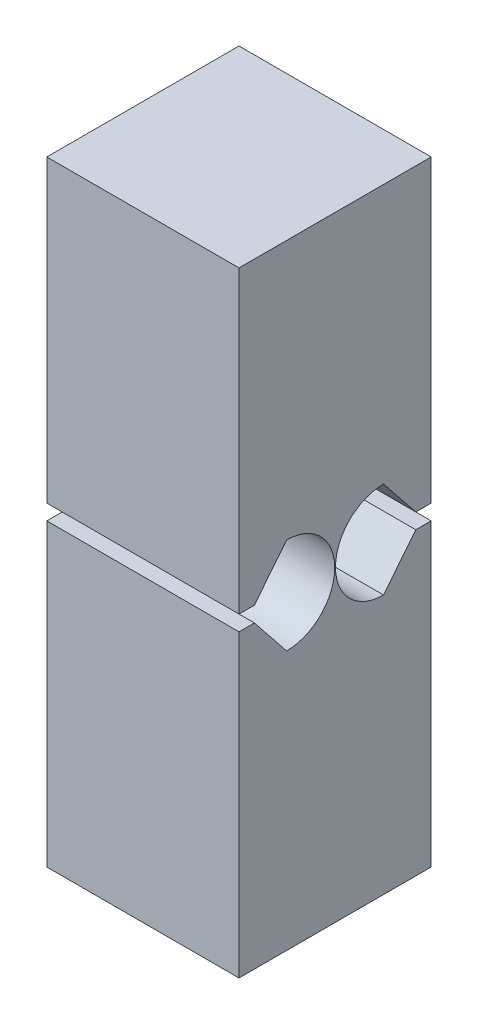
SolidWorks part; units mm, degrees
material "Beryllium Copper, UNS C17200"
ref_plane "Front Plane" through (0, 0, 0) normal (0, 0, 1) x (1, 0, 0)
ref_plane "Top Plane" through (0, 0, 0) normal (0, 1, 0) x (1, 0, 0)
ref_plane "Right Plane" through (0, 0, 0) normal (1, 0, 0) x (0, 0, -1)
sketch "Sketch1" plane through (0, 0, 0) normal (0, 1, 0) x (1, 0, 0)
  line L1 (-3.175, 3.175) -> (3.175, 3.175)
  line L2 (-3.175, 3.175) -> (-3.175, -3.175)
  line L3 (-3.175, -3.175) -> (3.175, -3.175)
  line L4 (3.175, 3.175) -> (3.175, -3.175)
  dimension "D1" = 3.175
  dimension "D2" = 3.175
  dimension "D3" = 3.175
  dimension "D4" = 3.175
extrude "Boss-Extrude1" add sketch "Sketch1" along normal mid plane 20.32
sketch "Sketch2" plane through (3.175, 0, 0) normal (1, 0, 0) x (0, 0, -1)
  line L0 (-3.175, 0.254) -> (-3.175, -0.254)
  line L1 (-3.175, 10.16) -> (-3.175, -10.16) construction
  line L2 (-3.175, -0.254) -> (-2.667, -0.254)
  line L3 (-2.667, -0.254) -> (-1.6002, -1.5875)
  line L4 (-3.175, 0.254) -> (-2.667, 0.254)
  line L5 (-2.667, 0.254) -> (-1.6002, 1.5875)
  arc A0 (-1.6002, 1.5875) -> (-1.6002, -1.5875) centre (-1.6002, 0) cw
  dimension "D1" = 0.254
  dimension "D2" = 0.254
  dimension "D3" = 0.508
  dimension "D4" = 0.508
extrude "Cut-Extrude1" cut sketch "Sketch2" against normal up to next (6.35 mm away)
mirror "Mirror1" about plane through (0, 0, 0) normal (0, 0, 1) of "Cut-Extrude1"
sketch "Sketch3" plane through (-3.175, 0, 0) normal (-1, 0, 0) x (0, 0, 1)
  line L0 (-3.175, -10.16) -> (3.175, -10.16) construction
  point P0 (0, 0)
  dimension "D1" = 10.16
